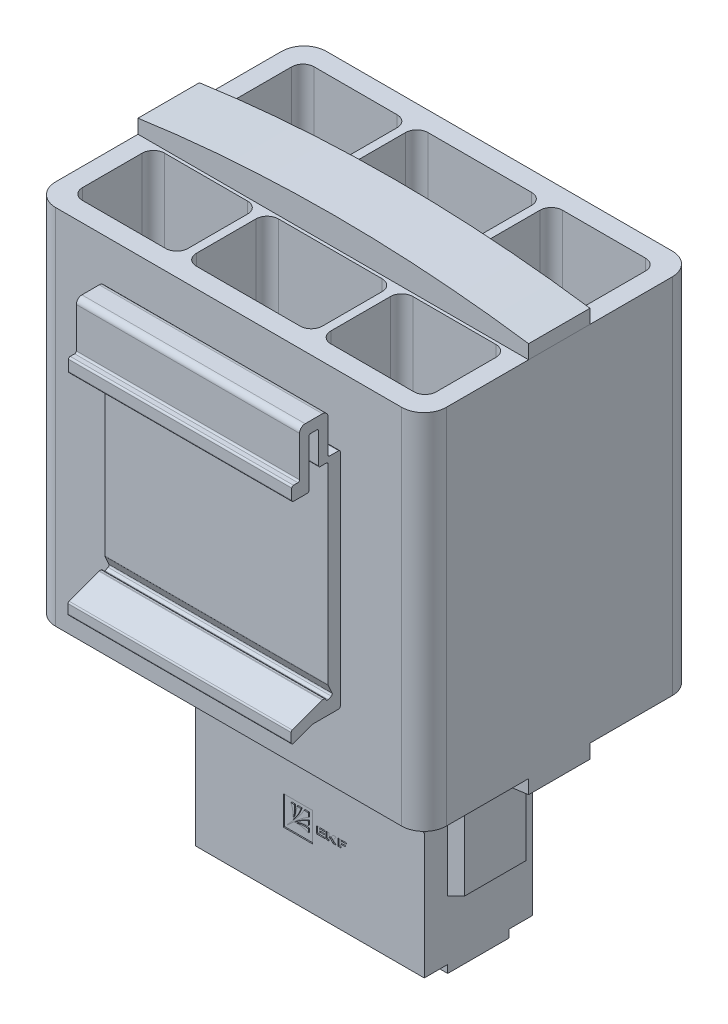
SolidWorks part; units mm, degrees
ref_plane "Спереди" through (0, 0, 0) normal (0, 0, 1) x (1, 0, 0)
ref_plane "Сверху" through (0, 0, 0) normal (0, 1, 0) x (1, 0, 0)
ref_plane "Справа" through (0, 0, 0) normal (1, 0, 0) x (0, 0, -1)
sketch "Эскиз1" plane through (0, 0, 0) normal (0, 0, 1) x (1, 0, 0)
  line L1 (-35, -32.5) -> (35, -32.5)
  line L2 (-35, -32.5) -> (-35, 32.5)
  line L3 (-35, 32.5) -> (35, 32.5)
  line L4 (35, -32.5) -> (35, 32.5)
  line L5 (-35, -32.5) -> (35, 32.5) construction
  line L6 (-35, 32.5) -> (35, -32.5) construction
  point P0 (0, 0)
  dimension "D1" = 70
  dimension "D2" = 65
extrude "Бобышка-Вытянуть1" add sketch "Эскиз1" along normal blind 48.5
sketch "Эскиз2" plane through (0, 32.5, 0) normal (0, 1, 0) x (1, 0, 0)
  line L0 (0, 0) -> (0, -10.85) construction
  line L1 (-11.3, -3.5) -> (11.3, -3.5)
  line L2 (-11.3, -3.5) -> (-11.3, -18.2)
  line L3 (-11.3, -18.2) -> (11.3, -18.2)
  line L4 (11.3, -3.5) -> (11.3, -18.2)
  line L5 (-11.3, -3.5) -> (11.3, -18.2) construction
  line L6 (-11.3, -18.2) -> (11.3, -3.5) construction
  line L7 (12.8, -3.5) -> (31.7, -3.5)
  line L8 (12.8, -3.5) -> (12.8, -18.2)
  line L9 (12.8, -18.2) -> (31.7, -18.2)
  line L10 (31.7, -3.5) -> (31.7, -18.2)
  line L11 (12.8, -3.5) -> (31.7, -18.2) construction
  line L12 (12.8, -18.2) -> (31.7, -3.5) construction
  line L13 (-31.7, -3.5) -> (-12.8, -3.5)
  line L14 (-31.7, -3.5) -> (-31.7, -18.2)
  line L15 (-31.7, -18.2) -> (-12.8, -18.2)
  line L16 (-12.8, -3.5) -> (-12.8, -18.2)
  line L17 (-31.7, -3.5) -> (-12.8, -18.2) construction
  line L18 (-31.7, -18.2) -> (-12.8, -3.5) construction
  line L19 (35, 0) -> (-35, 0) construction
  line L20 (-35, -24.25) -> (35, -24.25) construction
  line L21 (-35, -48.5) -> (-35, 0) construction
  line L22 (35, -48.5) -> (35, 0) construction
  line L23 (12.8, -30.3) -> (31.7, -30.3)
  line L24 (31.7, -45) -> (31.7, -30.3)
  line L25 (12.8, -45) -> (31.7, -45)
  line L26 (12.8, -45) -> (12.8, -30.3)
  line L27 (-11.3, -30.3) -> (11.3, -30.3)
  line L28 (11.3, -45) -> (11.3, -30.3)
  line L29 (-11.3, -45) -> (11.3, -45)
  line L30 (-11.3, -45) -> (-11.3, -30.3)
  line L31 (-31.7, -30.3) -> (-12.8, -30.3)
  line L32 (-12.8, -45) -> (-12.8, -30.3)
  line L33 (-31.7, -45) -> (-12.8, -45)
  line L34 (-31.7, -45) -> (-31.7, -30.3)
  point P0 (0, -10.85)
  point P5 (22.25, -10.85)
  point P10 (-22.25, -10.85)
  dimension "D1" = 22.6
  dimension "D2" = 18.9
  dimension "D3" = 1.5
  dimension "D4" = 1.5
  dimension "D5" = 3.5
  dimension "D6" = 14.7
extrude "Вырез-Вытянуть1" cut sketch "Эскиз2" against normal up to next
sketch "Эскиз3" plane through (0, 32.5, 0) normal (0, 1, 0) x (1, 0, 0)
  line L0 (35, -48.5) -> (35, 0) construction
  line L1 (-35, -29.75) -> (35, -29.75)
  line L2 (-35, -29.75) -> (-35, -18.75)
  line L3 (-35, -18.75) -> (35, -18.75)
  line L4 (35, -29.75) -> (35, -18.75)
  line L5 (-35, -29.75) -> (35, -18.75) construction
  line L6 (-35, -18.75) -> (35, -29.75) construction
  line L7 (0, 0) -> (0, -24.25) construction
  line L8 (35, 0) -> (-35, 0) construction
  line L9 (0, -24.25) -> (35, -24.25) construction
  point P0 (0, -24.25)
  point P15 (35, -24.25)
  dimension "D1" = 11
extrude "Бобышка-Вытянуть2" add sketch "Эскиз3" along normal blind 5 separate body
sketch "Эскиз4" plane through (0, 0, 29.75) normal (0, 0, 1) x (1, 0, 0)
  line L0 (-35, 37.5) -> (-35, 32.5) construction
  line L1 (35, 37.5) -> (35, 32.5) construction
  line L2 (-35, 37.5) -> (35, 37.5) construction
  line L3 (-35, 32.5) -> (35, 32.5) construction
  line L4 (-35, 35) -> (-35, 41)
  line L5 (-35, 41) -> (35, 41)
  line L6 (35, 41) -> (35, 35)
  arc A0 (-35, 35) -> (35, 35) centre (0, -208.75) cw
  point P3 (0, 37.5)
  dimension "D1" = 2.5
  dimension "D2" = 6
extrude "Вырез-Вытянуть4" cut sketch "Эскиз4" against normal up to surface (11 mm away) up to face at (0, 35, 18.75)
ref_plane "Плоскость1" through (0, 0, 0) normal (0, 1, 0) x (1, 0, 0)
mirror "Зеркальное отражение2" about plane through (0, 0, 0) normal (0, 1, 0) of "Вырез-Вытянуть4", "Бобышка-Вытянуть2"
ref_plane "Плоскость2" through (0, 0, 24.25) normal (0, 0, -1) x (-1, 0, 0)
sketch "Эскиз5" plane through (0, 0, 24.25) normal (0, 0, -1) x (-1, 0, 0)
  line L0 (-23.5, -36.3761) -> (-23.5, -56.5)
  line L1 (-23.5, -56.5) -> (-20.5, -58)
  line L2 (-20.5, -58) -> (-20.5, -70)
  line L3 (-20.5, -70) -> (20.5, -70)
  line L4 (20.5, -70) -> (20.5, -58)
  line L5 (20.5, -58) -> (23.5, -56.5)
  line L6 (23.5, -56.5) -> (23.5, -36.3761)
  line L7 (0, -37.5) -> (0, -70) construction
  line L8 (-35, -32.5) -> (35, -32.5) construction
  arc A0 (-35, -35) -> (35, -35) centre (0, 208.75) ccw construction
  arc A1 (-23.5, -36.3761) -> (23.5, -36.3761) centre (0, 208.75) ccw
  dimension "D1" = 37.5
  dimension "D2" = 41
  dimension "D3" = 47
  dimension "D4" = 12
  dimension "D5" = 13.5
extrude "Бобышка-Вытянуть3" add sketch "Эскиз5" along normal up to surface and the other way up to surface up to face at (0, -34.375, 18.75) other way up to face at (0, -34.375, 29.75)
sketch "Эскиз6" plane through (0, 0, 29.75) normal (0, 0, 1) x (1, 0, 0)
  line L0 (-20.5, -68.6) -> (-20.5, -41.6)
  line L1 (-20.5, -58) -> (-20.5, -70) construction
  line L2 (-20.5, -68.6) -> (20.5, -68.6)
  line L3 (20.5, -70) -> (20.5, -58) construction
  line L4 (20.5, -68.6) -> (20.5, -41.6)
  line L5 (-20.5, -70) -> (20.5, -70) construction
  arc A0 (-20.5, -41.6) -> (20.5, -41.6) centre (0, -81.125) cw
  point P11 (0, -36.6)
  dimension "D1" = 1.4
  dimension "D2" = 32
  dimension "D3" = 5
extrude "Бобышка-Вытянуть4" add sketch "Эскиз6" along normal blind 4.2
chamfer "Фаска1" distance 4 angle 45 1 edges at (0, -36.6, 33.95)
mirror "Зеркальное отражение3" about plane through (0, 0, 24.25) normal (0, 0, -1) of "Фаска1", "Бобышка-Вытянуть4"
sketch "Эскиз7" plane through (0, 0, 14.55) normal (0, 0, -1) x (-1, 0, 0)
  line L0 (0, -61.65) -> (0, -68.6) construction
  line L1 (-5.65, -57.4) -> (5.65, -57.4)
  line L2 (-5.65, -57.4) -> (-5.65, -65.9)
  line L3 (-5.65, -65.9) -> (5.65, -65.9)
  line L4 (5.65, -57.4) -> (5.65, -65.9)
  line L5 (-5.65, -57.4) -> (5.65, -65.9) construction
  line L6 (-5.65, -65.9) -> (5.65, -57.4) construction
  line L7 (-18.15, -57.4) -> (-6.85, -57.4)
  line L8 (-18.15, -57.4) -> (-18.15, -65.9)
  line L9 (-18.15, -65.9) -> (-6.85, -65.9)
  line L10 (-6.85, -57.4) -> (-6.85, -65.9)
  line L11 (-18.15, -57.4) -> (-6.85, -65.9) construction
  line L12 (-18.15, -65.9) -> (-6.85, -57.4) construction
  line L13 (6.85, -57.4) -> (18.15, -57.4)
  line L14 (6.85, -57.4) -> (6.85, -65.9)
  line L15 (6.85, -65.9) -> (18.15, -65.9)
  line L16 (18.15, -57.4) -> (18.15, -65.9)
  line L17 (6.85, -57.4) -> (18.15, -65.9) construction
  line L18 (6.85, -65.9) -> (18.15, -57.4) construction
  line L19 (20.5, -68.6) -> (-20.5, -68.6) construction
  line L20 (20.5, -68.6) -> (-20.5, -68.6) construction
  point P0 (0, -61.65)
  point P5 (-12.5, -61.65)
  point P10 (12.5, -61.65)
  dimension "D1" = 11.3
  dimension "D2" = 1.2
  dimension "D3" = 1.2
  dimension "D4" = 2.7
  dimension "D5" = 8.5
extrude "Бобышка-Вытянуть5" add sketch "Эскиз7" along normal blind 2 draft 12
sketch "Эскиз9" plane through (0, -70, 0) normal (0, -1, 0) x (1, 0, 0)
  line L0 (0, 27.25) -> (0, 0) construction
  line L1 (-14.5, 29.75) -> (-10.5, 29.75)
  line L2 (-14.5, 29.75) -> (-14.5, 24.75)
  line L3 (-14.5, 24.75) -> (-10.5, 24.75)
  line L4 (-10.5, 29.75) -> (-10.5, 24.75)
  line L5 (-14.5, 29.75) -> (-10.5, 24.75) construction
  line L6 (-14.5, 24.75) -> (-10.5, 29.75) construction
  line L7 (-2, 29.75) -> (2, 29.75)
  line L8 (-2, 29.75) -> (-2, 24.75)
  line L9 (-2, 24.75) -> (2, 24.75)
  line L10 (2, 29.75) -> (2, 24.75)
  line L11 (-2, 29.75) -> (2, 24.75) construction
  line L12 (-2, 24.75) -> (2, 29.75) construction
  line L13 (10.5, 29.75) -> (14.5, 29.75)
  line L14 (10.5, 29.75) -> (10.5, 24.75)
  line L15 (10.5, 24.75) -> (14.5, 24.75)
  line L16 (14.5, 29.75) -> (14.5, 24.75)
  line L17 (10.5, 29.75) -> (14.5, 24.75) construction
  line L18 (10.5, 24.75) -> (14.5, 29.75) construction
  line L19 (-12.5, 27.25) -> (0, 27.25) construction
  line L20 (0, 27.25) -> (12.5, 27.25) construction
  line L21 (-12.5, 12.55) -> (-12.5, 27.25) construction
  line L22 (-7.2751, 12.55) -> (-17.7249, 12.55) construction
  line L23 (12.5, 27.25) -> (12.5, 12.55) construction
  line L24 (17.7249, 12.55) -> (7.2751, 12.55) construction
  line L27 (-20.5, 29.75) -> (20.5, 29.75) construction
  point P0 (-12.5, 27.25)
  point P5 (0, 27.25)
  point P10 (12.5, 27.25)
  dimension "D1" = 4
  dimension "D2" = 5
extrude "Вырез-Вытянуть5" cut sketch "Эскиз9" against normal blind 7
sketch "Эскиз10" plane through (0, -70, 0) normal (0, -1, 0) x (1, 0, 0)
  line L0 (-20.5, 18.75) -> (20.5, 18.75) construction
  line L1 (-14.5, 24.75) -> (-10.5, 24.75)
  line L2 (-14.5, 24.75) -> (-14.5, 18.75)
  line L3 (-14.5, 18.75) -> (-10.5, 18.75)
  line L4 (-10.5, 24.75) -> (-10.5, 18.75)
  line L5 (-20.5, 18.75) -> (20.5, 18.75) construction
  line L6 (-2, 24.75) -> (2, 24.75)
  line L7 (-2, 24.75) -> (-2, 18.75)
  line L8 (-2, 18.75) -> (2, 18.75)
  line L9 (2, 24.75) -> (2, 18.75)
  line L10 (10.5, 24.75) -> (14.5, 24.75)
  line L11 (10.5, 24.75) -> (10.5, 18.75)
  line L12 (10.5, 18.75) -> (14.5, 18.75)
  line L13 (14.5, 24.75) -> (14.5, 18.75)
  line L14 (14.5, 24.75) -> (14.5, 29.75) construction
  line L15 (2, 24.75) -> (2, 29.75) construction
  line L16 (-10.5, 24.75) -> (-10.5, 29.75) construction
extrude "Вырез-Вытянуть6" cut sketch "Эскиз10" against normal up to surface (1.4 mm away) up to face at (0, -68.6, 16.65)
ref_plane "Плоскость3" through (0, 0, 0) normal (-1, 0, 0) x (0, 0, 1)
sketch "Эскиз11" plane through (0, 0, 0) normal (-1, 0, 0) x (0, 0, 1)
  line L0 (48.8, -19.7) -> (53.4465, -19.7)
  line L1 (53.5502, -19.7185) -> (56.8963, -20.9513)
  line L2 (57.3, -20.6698) -> (57.3, -19.0712)
  line L3 (57.1037, -18.7897) -> (51.7533, -16.8185)
  line L4 (51.6496, -16.8) -> (51.3956, -16.8)
  line L5 (51.1229, -16.975) -> (51.0531, -17.1273)
  line L6 (50.6554, -17.275) -> (50.1099, -17.025)
  line L7 (49.9622, -16.6273) -> (50.6727, -15.0772)
  line L8 (50.7, -14.9522) -> (50.7, 19.3)
  line L9 (51, 19.6) -> (52.1, 19.6)
  line L10 (52.4, 19.9) -> (52.4, 25.3)
  line L11 (52.7, 25.6) -> (53.8, 25.6)
  line L12 (54.1, 25.3) -> (54.1, 16.9)
  line L13 (54.4, 16.6) -> (56.9, 16.6)
  line L14 (57.2, 16.9) -> (57.2, 18.8)
  line L15 (56.9, 19.1) -> (56.1, 19.1)
  line L16 (55.8, 19.4) -> (55.8, 26.6)
  line L17 (54.8, 27.6) -> (51.7, 27.6)
  line L18 (50.7, 26.6) -> (50.7, 20.7)
  line L19 (50.4, 20.4) -> (48.8, 20.4)
  line L20 (48.5, 20.1) -> (48.5, -19.4)
  line L21 (48.5, 32.5) -> (48.5, -32.5) construction
  line L22 (48.5, 32.5) -> (0, 32.5) construction
  arc A0 (48.8, -19.7) -> (48.5, -19.4) centre (48.8, -19.4) cw
  arc A1 (53.4465, -19.7) -> (53.5502, -19.7185) centre (53.4465, -20) cw
  arc A2 (57.3, -19.0712) -> (57.1037, -18.7897) centre (57, -19.0712) ccw
  arc A3 (56.8963, -20.9513) -> (57.3, -20.6698) centre (57, -20.6698) ccw
  arc A4 (51.7533, -16.8185) -> (51.6496, -16.8) centre (51.6496, -17.1) ccw
  arc A5 (51.3956, -16.8) -> (51.1229, -16.975) centre (51.3956, -17.1) ccw
  arc A6 (50.6727, -15.0772) -> (50.7, -14.9522) centre (50.4, -14.9522) ccw
  arc A7 (50.1099, -17.025) -> (49.9622, -16.6273) centre (50.2349, -16.7523) cw
  arc A8 (51.0531, -17.1273) -> (50.6554, -17.275) centre (50.7804, -17.0023) cw
  arc A9 (54.1, 16.9) -> (54.4, 16.6) centre (54.4, 16.9) ccw
  arc A10 (56.9, 16.6) -> (57.2, 16.9) centre (56.9, 16.9) ccw
  arc A11 (57.2, 18.8) -> (56.9, 19.1) centre (56.9, 18.8) ccw
  arc A12 (56.1, 19.1) -> (55.8, 19.4) centre (56.1, 19.4) cw
  arc A13 (48.8, 20.4) -> (48.5, 20.1) centre (48.8, 20.1) ccw
  arc A14 (50.7, 20.7) -> (50.4, 20.4) centre (50.4, 20.7) cw
  arc A15 (50.7, 19.3) -> (51, 19.6) centre (51, 19.3) cw
  arc A16 (52.1, 19.6) -> (52.4, 19.9) centre (52.1, 19.9) ccw
  arc A17 (52.4, 25.3) -> (52.7, 25.6) centre (52.7, 25.3) cw
  arc A18 (53.8, 25.6) -> (54.1, 25.3) centre (53.8, 25.3) cw
  arc A19 (51.7, 27.6) -> (50.7, 26.6) centre (51.7, 26.6) ccw
  arc A20 (55.8, 26.6) -> (54.8, 27.6) centre (54.8, 26.6) ccw
  point P21 (53.25, 25.6)
  point P22 (53.25, 27.6)
  point P65 (48.5, 20.1)
  dimension "D7" = 0.3
  dimension "D8" = 1
  dimension "D1" = 2.1
  dimension "D2" = 2.2
  dimension "D3" = 47.3
  dimension "D4" = 6.5
  dimension "D5" = 2
  dimension "D6" = 11
  dimension "D9" = 7.2
  dimension "D10" = 12.4
extrude "Бобышка-Вытянуть6" add sketch "Эскиз11" along normal mid plane 40
fillet "Скругление1" radius 4 4 edges at (35, 0, 0) (35, 0, 48.5) (-35, 0, 0) (-35, 0, 48.5)
fillet "Скругление2" radius 2 24 edges at (-12.8, 0, 3.5) (-12.8, 0, 18.2) (-31.7, 0, 18.2) (-31.7, 0, 3.5) (-11.3, 0, 3.5) (-11.3, 0, 18.2) (11.3, 0, 18.2) (11.3, 0, 3.5) (31.7, 0, 18.2) (12.8, 0, 18.2) (12.8, 0, 3.5) (31.7, 0, 3.5) (31.7, 0, 30.3) (12.8, 0, 30.3) (12.8, 0, 45) (31.7, 0, 45) (11.3, 0, 45) (11.3, 0, 30.3) (-11.3, 0, 30.3) (-11.3, 0, 45) (-12.8, 0, 45) (-12.8, 0, 30.3) (-31.7, 0, 30.3) (-31.7, 0, 45)
sketch "Эскиз12" plane through (0, 0, 33.95) normal (0, 0, 1) x (1, 0, 0)
  line L0 (-4.7623, -57.8049) -> (0.4559, -57.8049)
  line L1 (0.4559, -57.8049) -> (0.4559, -52.5968)
  line L2 (0.4559, -52.5968) -> (-4.7623, -52.5968)
  line L3 (-4.7623, -52.5968) -> (-4.7623, -57.8049)
  line L4 (-0.2878, -56.4724) -> (-0.2878, -55.8157)
  line L5 (-0.2878, -55.3576) -> (-0.2878, -54.6088)
  line L6 (-0.2878, -54.0846) -> (-0.2878, -53.3358)
  line L7 (-0.2878, -53.3358) -> (-1.0366, -53.3358)
  line L8 (-1.5608, -53.3358) -> (-2.3096, -53.3358)
  line L9 (-2.7678, -53.3358) -> (-3.4245, -53.3358)
  line L10 (4.9957, -54.6088) -> (4.9957, -55.8788)
  line L11 (4.9957, -55.8788) -> (5.5487, -55.8788)
  line L12 (5.5487, -55.8788) -> (5.5487, -55.3028)
  line L13 (5.5487, -55.3028) -> (6.4242, -55.3028)
  line L14 (6.4242, -55.3028) -> (6.4242, -55.1185)
  line L15 (6.4242, -55.1185) -> (5.5487, -55.1185)
  line L16 (5.5487, -55.1185) -> (5.5487, -54.8017)
  line L17 (5.5487, -54.8017) -> (6.5221, -54.8017)
  line L18 (6.5221, -54.8017) -> (6.5221, -54.6088)
  line L19 (6.5221, -54.6088) -> (4.9957, -54.6088)
  line L20 (3.4256, -55.3146) -> (3.5753, -55.3146)
  line L21 (3.7486, -55.3966) -> (4.1255, -55.879)
  line L22 (4.1255, -55.879) -> (4.7015, -55.879)
  line L23 (4.7015, -55.879) -> (4.2295, -55.2749)
  line L24 (4.2295, -55.2395) -> (4.7192, -54.6127)
  line L25 (4.7192, -54.6127) -> (4.138, -54.6127)
  line L26 (4.138, -54.6127) -> (3.8365, -54.9985)
  line L27 (3.6848, -55.1099) -> (3.4256, -55.1099)
  line L28 (3.4256, -55.1099) -> (3.4256, -54.6088)
  line L29 (3.4256, -54.6088) -> (2.8714, -54.6088)
  line L30 (2.8714, -54.6088) -> (2.8714, -55.5389)
  line L31 (2.9978, -55.879) -> (3.4256, -55.879)
  line L32 (3.4256, -55.879) -> (3.4256, -55.3146)
  line L33 (1.713, -55.3115) -> (2.6058, -55.3115)
  line L34 (2.6058, -55.3115) -> (2.6058, -55.1099)
  line L35 (2.6058, -55.1099) -> (1.713, -55.1099)
  line L36 (1.713, -55.1099) -> (1.713, -54.8104)
  line L37 (1.713, -54.8104) -> (2.6922, -54.8104)
  line L38 (2.6922, -54.8104) -> (2.6922, -54.6088)
  line L39 (2.6922, -54.6088) -> (1.1658, -54.6088)
  line L40 (1.1658, -54.6088) -> (1.1658, -55.5389)
  line L41 (1.3167, -55.879) -> (2.6922, -55.879)
  line L42 (2.6922, -55.879) -> (2.6922, -55.6859)
  line L43 (2.6922, -55.6859) -> (1.713, -55.6859)
  line L44 (1.713, -55.6859) -> (1.713, -55.3115)
  arc A0 (-2.2891, -55.9741) -> (-2.3108, -56.0028) centre (-2.282, -56.002) ccw
  arc A1 (-2.3101, -56.0114) -> (-2.28, -56.0366) centre (-2.2815, -56.0078) ccw
  arc A2 (-2.7273, -56.0263) -> (-2.7365, -56.0411) centre (-2.7086, -56.0482) ccw
  arc A3 (-2.7051, -56.0853) -> (-2.6905, -56.0813) centre (-2.7052, -56.0565) ccw
  arc A4 (-4.0035, -56.9961) -> (-3.941, -57.0444) centre (-3.9723, -57.0203) ccw
  arc A5 (-3.0334, -55.7384) -> (-3.0374, -55.7531) centre (-3.0086, -55.7531) ccw
  arc A6 (-2.9932, -55.7844) -> (-2.9783, -55.7752) centre (-3.0003, -55.7565) ccw
  arc A7 (-2.9886, -55.3279) -> (-2.9635, -55.358) centre (-2.9599, -55.3294) ccw
  arc A8 (-2.9549, -55.3587) -> (-2.9262, -55.337) centre (-2.9541, -55.3299) ccw
  arc A9 (4.2295, -55.2395) -> (4.2295, -55.2749) centre (4.2522, -55.2572) ccw
  arc A10 (1.1658, -55.5389) -> (1.2031, -55.7428) centre (1.7418, -55.5389) ccw
  arc A11 (1.275, -55.8611) -> (1.3167, -55.879) centre (1.3167, -55.8214) ccw
  spline S0 degree 3 poles (-2.3108, -56.0028) (-2.3107, -56.0055) (-2.3104, -56.0083) (-2.3101, -56.0112) (-2.3101, -56.0114) knots 0 0 0 0 0.917925 1 1 1 1 weights 1 1 1 1 1
  spline S1 degree 3 poles (-2.28, -56.0366) (-2.1578, -56.0302) (-1.9642, -56.0247) (-1.7062, -56.0429) (-1.5152, -56.0764) (-1.3316, -56.1033) (-1.1555, -56.1447) (-0.9802, -56.1841) (-0.8245, -56.2398) (-0.6821, -56.2886) (-0.5586, -56.3424) (-0.428, -56.4027) (-0.3378, -56.4431) (-0.2878, -56.4724) knots 0 0 0 0 0.17778 0.281267 0.375033 0.459576 0.550813 0.637751 0.720424 0.790855 0.856523 0.915971 1 1 1 1 weights 1 1 1 1 1 1 1 1 1 1 1 1 1 1
  spline S2 degree 3 poles (-0.2878, -55.8157) (-0.3641, -55.8032) (-0.4985, -55.7967) (-0.6992, -55.7882) (-0.8823, -55.7781) (-1.0785, -55.7775) (-1.278, -55.7903) (-1.4931, -55.8038) (-1.7021, -55.8301) (-1.895, -55.867) (-2.0896, -55.9069) (-2.2145, -55.9553) (-2.2891, -55.9741) knots 0 0 0 0 0.114393 0.199277 0.298132 0.386384 0.490042 0.594519 0.706019 0.802157 0.885931 1 1 1 1 weights 1 1 1 1 1 1 1 1 1 1 1 1 1
  spline S3 degree 3 poles (-0.2878, -54.6088) (-0.5329, -54.6925) (-0.8841, -54.8599) (-1.3505, -55.0916) (-1.6718, -55.2895) (-1.9725, -55.4796) (-2.2214, -55.6507) (-2.4266, -55.7958) (-2.5821, -55.921) (-2.6834, -55.9889) (-2.7273, -56.0263) knots 0 0 0 0 0.273618 0.411874 0.551161 0.673016 0.788626 0.871078 0.939011 1 1 1 1 weights 1 1 1 1 1 1 1 1 1 1 1
  spline S4 degree 3 poles (-2.7365, -56.0411) (-2.7393, -56.052) (-2.741, -56.0785) (-2.7159, -56.0853) (-2.7051, -56.0853) knots 0 0 0 0 0.510001 1 1 1 1 weights 1 1 1 1 1
  spline S5 degree 3 poles (-2.6905, -56.0813) (-2.5839, -56.0182) (-2.4049, -55.9256) (-2.151, -55.8002) (-1.9301, -55.7027) (-1.6944, -55.6186) (-1.4515, -55.5398) (-1.1994, -55.4816) (-0.9577, -55.435) (-0.7392, -55.3998) (-0.5191, -55.3773) (-0.3726, -55.3658) (-0.2878, -55.3576) knots 0 0 0 0 0.146583 0.238456 0.335283 0.432158 0.534641 0.637315 0.738125 0.826097 0.899195 1 1 1 1 weights 1 1 1 1 1 1 1 1 1 1 1 1 1
  spline S6 degree 3 poles (-1.0366, -53.3358) (-1.083, -53.4462) (-1.1753, -53.6131) (-1.3197, -53.8436) (-1.4521, -54.0363) (-1.5929, -54.2388) (-1.7418, -54.4405) (-1.8988, -54.6537) (-2.0732, -54.8663) (-2.2483, -55.0792) (-2.4156, -55.2772) (-2.5682, -55.459) (-2.7237, -55.6261) (-2.914, -55.8304) (-3.3437, -56.2867) (-3.7103, -56.6959) (-4.0035, -56.9961) knots 0 0 0 0 0.075851 0.120866 0.172576 0.224175 0.277338 0.331656 0.392142 0.451757 0.506605 0.556596 0.602323 0.651423 0.733779 1 1 1 1 weights 1 1 1 1 1 1 1 1 1 1 1 1 1 1 1 1 1
  spline S7 degree 3 poles (-3.941, -57.0444) (-3.6429, -56.7537) (-3.2363, -56.3893) (-2.7825, -55.9619) (-2.5781, -55.7716) (-2.411, -55.6161) (-2.2293, -55.4635) (-2.0313, -55.2962) (-1.8184, -55.1211) (-1.6058, -54.9468) (-1.3926, -54.7897) (-1.1909, -54.6408) (-0.9884, -54.5) (-0.7957, -54.3676) (-0.5652, -54.2233) (-0.3983, -54.1309) (-0.2878, -54.0846) knots 0 0 0 0 0.264644 0.347178 0.396382 0.442208 0.492307 0.547272 0.607015 0.667632 0.722066 0.775343 0.827053 0.878874 0.923986 1 1 1 1 weights 1 1 1 1 1 1 1 1 1 1 1 1 1 1 1 1 1
  spline S8 degree 3 poles (-3.0374, -55.7531) (-3.0374, -55.7638) (-3.0306, -55.7889) (-3.004, -55.7872) (-2.9932, -55.7844) knots 0 0 0 0 0.489999 1 1 1 1 weights 1 1 1 1 1
  spline S9 degree 3 poles (-2.9783, -55.7752) (-2.941, -55.7313) (-2.8731, -55.63) (-2.7479, -55.4745) (-2.6028, -55.2693) (-2.4317, -55.0204) (-2.2416, -54.7197) (-2.0437, -54.3984) (-1.812, -53.932) (-1.6446, -53.5808) (-1.5608, -53.3358) knots 0 0 0 0 0.060989 0.128922 0.211374 0.326984 0.448839 0.588126 0.726382 1 1 1 1 weights 1 1 1 1 1 1 1 1 1 1 1
  spline S10 degree 3 poles (-2.3096, -53.3358) (-2.3179, -53.4205) (-2.3294, -53.567) (-2.3518, -53.7871) (-2.3871, -54.0056) (-2.4337, -54.2474) (-2.4919, -54.4994) (-2.5707, -54.7423) (-2.6548, -54.978) (-2.7523, -55.1989) (-2.8777, -55.4528) (-2.9703, -55.6318) (-3.0334, -55.7384) knots 0 0 0 0 0.100805 0.173903 0.261875 0.362685 0.465359 0.567842 0.664717 0.761544 0.853417 1 1 1 1 weights 1 1 1 1 1 1 1 1 1 1 1 1 1
  spline S11 degree 3 poles (-3.4245, -53.3358) (-3.3952, -53.3857) (-3.3548, -53.4759) (-3.2945, -53.6065) (-3.2407, -53.73) (-3.1919, -53.8724) (-3.1362, -54.0281) (-3.0968, -54.2035) (-3.0554, -54.3795) (-3.0285, -54.5631) (-2.995, -54.7541) (-2.9768, -55.0121) (-2.9823, -55.2057) (-2.9886, -55.3279) knots 0 0 0 0 0.084029 0.143477 0.209145 0.279576 0.362249 0.449187 0.540424 0.624967 0.718733 0.82222 1 1 1 1 weights 1 1 1 1 1 1 1 1 1 1 1 1 1 1
  spline S12 degree 3 poles (-2.9635, -55.358) (-2.9633, -55.358) (-2.9604, -55.3584) (-2.9575, -55.3587) (-2.9549, -55.3587) knots 0 0 0 0 0.082075 1 1 1 1 weights 1 1 1 1 1
  spline S13 degree 3 poles (-2.9262, -55.337) (-2.9073, -55.2624) (-2.8589, -55.1375) (-2.8191, -54.9429) (-2.7822, -54.75) (-2.7559, -54.541) (-2.7424, -54.3259) (-2.7296, -54.1264) (-2.7302, -53.9303) (-2.7403, -53.7471) (-2.7488, -53.5464) (-2.7553, -53.412) (-2.7678, -53.3358) knots 0 0 0 0 0.114069 0.197843 0.293981 0.405481 0.509958 0.613616 0.701868 0.800723 0.885607 1 1 1 1 weights 1 1 1 1 1 1 1 1 1 1 1 1 1
  spline S14 degree 3 poles (3.5753, -55.3146) (3.6105, -55.3171) (3.6771, -55.3303) (3.7305, -55.372) (3.7486, -55.3966) knots 0 0 0 0 0.539816 1 1 1 1 weights 1 1 1 1 1
  spline S15 degree 3 poles (3.8365, -54.9985) (3.8087, -55.0355) (3.7843, -55.0537) (3.7212, -55.1005) (3.6848, -55.1099) knots 0 0 0 0 0.375989 1 1 1 1 weights 1 1 1 1 1
  spline S16 degree 3 poles (2.8714, -55.5389) (2.8729, -55.5791) (2.884, -55.6372) (2.9033, -55.7123) (2.9252, -55.7602) (2.9533, -55.8175) (2.9797, -55.855) (2.9978, -55.879) knots 0 0 0 0 0.326178 0.481344 0.628375 0.754487 1 1 1 1 weights 1 1 1 1 1 1 1 1
  spline S17 degree 3 poles (1.2031, -55.7428) (1.2053, -55.7488) (1.217, -55.7775) (1.2397, -55.8183) (1.2644, -55.85) (1.275, -55.8611) knots 0 0 0 0 0.137108 0.669562 1 1 1 1 weights 1 1 1 1 1 1
extrude "Вырез-Вытянуть7" cut sketch "Эскиз12" against normal blind 0.2
